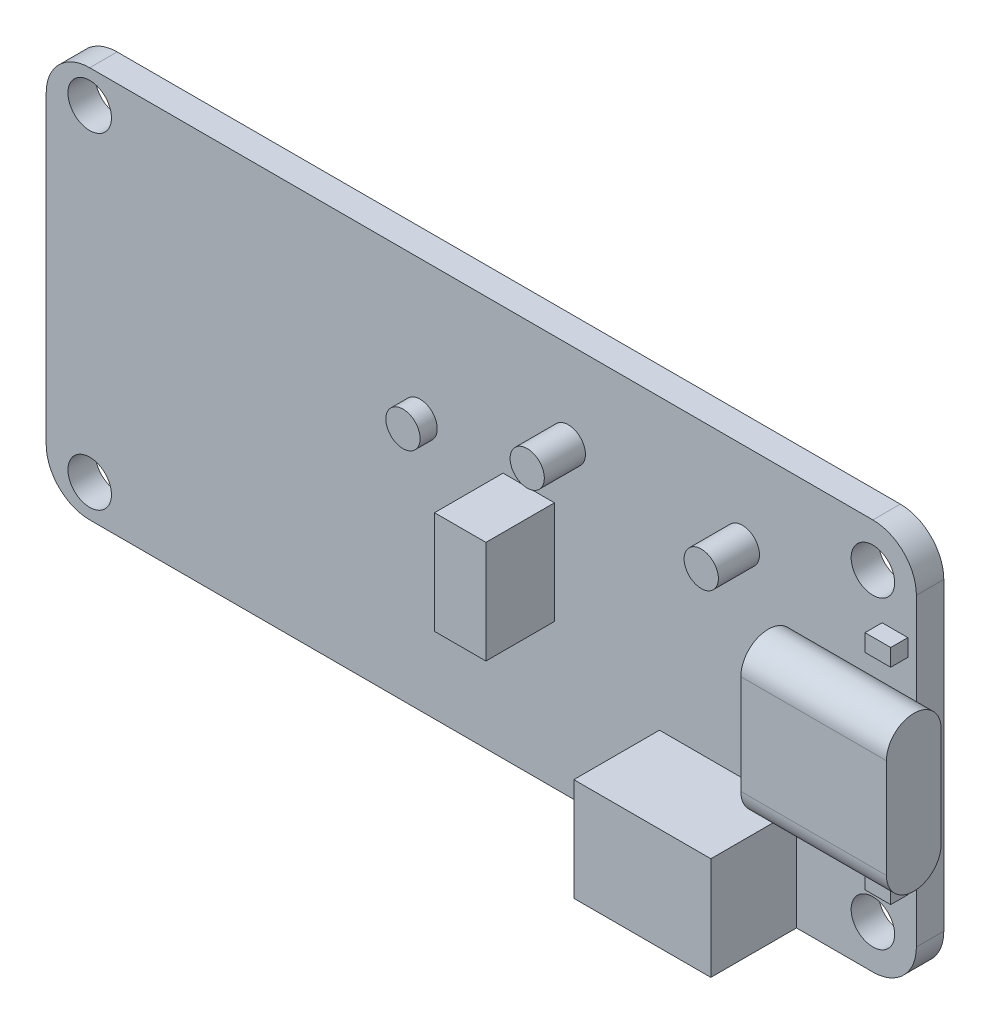
SolidWorks part; units mm, degrees
material "Unlegierter Baustahl"
ref_plane "Ebene vorne" through (0, 0, 0) normal (0, 0, 1) x (1, 0, 0)
ref_plane "Ebene oben" through (0, 0, 0) normal (0, 1, 0) x (1, 0, 0)
ref_plane "Ebene rechts" through (0, 0, 0) normal (1, 0, 0) x (0, 0, -1)
sketch "Skizze1" plane through (0, 0, 0) normal (0, 0, 1) x (1, 0, 0)
  line L1 (-22.86, -11.43) -> (22.86, -11.43)
  line L2 (-25.4, -8.89) -> (-25.4, 8.89)
  line L3 (-22.86, 11.43) -> (22.86, 11.43)
  line L4 (25.4, -8.89) -> (25.4, 8.89)
  line L5 (-25.4, -11.43) -> (25.4, 11.43) construction
  line L6 (-25.4, 11.43) -> (25.4, -11.43) construction
  arc A0 (-25.4, 8.89) -> (-22.86, 11.43) centre (-22.86, 8.89) cw
  arc A1 (-22.86, -11.43) -> (-25.4, -8.89) centre (-22.86, -8.89) cw
  arc A2 (22.86, -11.43) -> (25.4, -8.89) centre (22.86, -8.89) ccw
  arc A3 (22.86, 11.43) -> (25.4, 8.89) centre (22.86, 8.89) cw
  point P0 (0, 0)
  dimension "D3" = 2.54
  dimension "D1" = 50.8
  dimension "D2" = 22.86
extrude "board" add sketch "Skizze1" along normal blind 1.6
hole_wizard "Durchgangsloch für M21" positions "Skizze2" profile "Skizze3" hole size "M2" standard "DIN" end condition through all
sketch "Skizze2" plane through (0, 0, 1.6) normal (0, 0, 1) x (1, 0, 0)
  line L4 (22.86, -9.525) -> (-22.86, -9.525) construction
  line L5 (22.86, -9.525) -> (22.86, 9.525) construction
  line L6 (22.86, 9.525) -> (-22.86, 9.525) construction
  line L7 (-22.86, -9.525) -> (-22.86, 9.525) construction
  line L8 (22.86, -9.525) -> (-22.86, 9.525) construction
  line L9 (22.86, 9.525) -> (-22.86, -9.525) construction
  point P12 (-22.86, 9.525)
  point P14 (-22.86, -9.525)
  point P123 (22.86, 8.89)
  point P125 (22.86, -8.89)
  dimension "D1" = 19.05
  dimension "D2" = 45.72
  dimension "D3" = 8.89
  dimension "D4" = 8.89
sketch "Skizze3" plane through (-22.86, 9.525, 1.6) normal (1, 0, 0) x (0, -1, 0)
  line L0 (0, 0) -> (0, 1.6)
  line L1 (0, 1.6) -> (1.27, 1.6)
  line L2 (1.27, 1.6) -> (1.27, 0)
  line L5 (1.27, 0) -> (0, 0)
  line L11 (0, -6.35) -> (0, 107.95) construction
  dimension "Bohrerdurchmesser" = 2.54
  dimension "Bohrungstiefe" = 1.6
sketch "Skizze4" plane through (25.4, 0, 0) normal (1, 0, 0) x (0, 0, -1)
  line L0 (-3.25, -2.9) -> (-3.25, 2.9) construction
  line L1 (-4.85, -2.9) -> (-4.85, 2.9)
  line L2 (-1.65, -2.9) -> (-1.65, 2.9)
  line L3 (-1.6, -8.89) -> (-1.6, 8.89) construction
  arc A0 (-4.85, -2.9) -> (-1.65, -2.9) centre (-3.25, -2.9) ccw
  arc A1 (-1.65, 2.9) -> (-4.85, 2.9) centre (-3.25, 2.9) ccw
  point P2 (-3.25, 0)
  point P7 (-3.25, 4.5)
  point P8 (-3.25, -4.5)
  dimension "D1" = 9
  dimension "D2" = 0.05
  dimension "D3" = 3.2
extrude "usbc" add sketch "Skizze4" along normal blind 1.5 and the other way blind 7 separate body
sketch "Skizze5" plane through (0, -11.43, 0) normal (0, -1, 0) x (1, 0, 0)
  line L0 (-22.86, 1.6) -> (22.86, 1.6) construction
  line L1 (10.4, 6.6) -> (18.4, 6.6)
  line L2 (10.4, 6.6) -> (10.4, 1.6)
  line L3 (10.4, 1.6) -> (18.4, 1.6)
  line L4 (18.4, 6.6) -> (18.4, 1.6)
  line L5 (10.4, 6.6) -> (18.4, 1.6) construction
  line L6 (10.4, 1.6) -> (18.4, 6.6) construction
  line L8 (25.4, 1.6) -> (25.4, 0) construction
  point P0 (14.4, 4.1)
  dimension "D1" = 5
  dimension "D2" = 15
  dimension "D3" = 8
extrude "battery" add sketch "Skizze5" against normal blind 6
sketch "Skizze6" plane through (0, 0, 1.6) normal (0, 0, 1) x (1, 0, 0)
  line L0 (25.4, -8.89) -> (25.4, 8.89) construction
  line L1 (22.86, 11.43) -> (-22.86, 11.43) construction
  line L2 (18.4, -11.43) -> (22.86, -11.43) construction
  circle A0 centre (15.24, 6.35) radius 1
  circle A1 centre (5.08, 6.35) radius 1
  dimension "D6" = 2
  dimension "D1" = 10.16
  dimension "D2" = 20.32
  dimension "D3" = 17.78
  dimension "D5" = 5.08
extrude "buttons" add sketch "Skizze6" along normal blind 2.4
sketch "Skizze7" plane through (0, 0, 1.6) normal (0, 0, 1) x (1, 0, 0)
  line L0 (25.4, -8.89) -> (25.4, 8.89) construction
  line L1 (4.27, -3) -> (1.27, -3)
  line L2 (4.27, -3) -> (4.27, 3)
  line L3 (4.27, 3) -> (1.27, 3)
  line L4 (1.27, -3) -> (1.27, 3)
  line L5 (4.27, -3) -> (1.27, 3) construction
  line L6 (4.27, 3) -> (1.27, -3) construction
  point P0 (2.77, 0)
  dimension "D1" = 24.13
  dimension "D2" = 6
  dimension "D3" = 3
extrude "qwiic" add sketch "Skizze7" along normal blind 4
sketch "Skizze8" plane through (0, 0, 1.6) normal (0, 0, 1) x (1, 0, 0)
  line L1 (-4.572, 2.318) -> (-2.572, 2.318) construction
  line L2 (-4.572, 2.318) -> (-4.572, 4.318) construction
  line L3 (-4.572, 4.318) -> (-2.572, 4.318) construction
  line L4 (-2.572, 2.318) -> (-2.572, 4.318) construction
  line L5 (-4.572, 2.318) -> (-2.572, 4.318) construction
  line L6 (-4.572, 4.318) -> (-2.572, 2.318) construction
  line L7 (25.4, -8.89) -> (25.4, 8.89) construction
  line L8 (22.86, 11.43) -> (-22.86, 11.43) construction
  circle A0 centre (-3.572, 3.318) radius 1
  point P0 (-3.572, 3.318)
  dimension "D1" = 29.972
  dimension "D2" = 2
  dimension "D3" = 2
  dimension "D4" = 7.112
extrude "neopixel" add sketch "Skizze8" along normal blind 1
sketch "Skizze9" plane through (0, 0, 1.6) normal (0, 0, 1) x (1, 0, 0)
  line L0 (25.4, -8.89) -> (25.4, 8.89) construction
  line L1 (23.4, 5.5) -> (24.9, 5.5)
  line L2 (23.4, 5.5) -> (23.4, 6.5)
  line L3 (23.4, 6.5) -> (24.9, 6.5)
  line L4 (24.9, 5.5) -> (24.9, 6.5)
  line L5 (23.4, 5.5) -> (24.9, 6.5) construction
  line L6 (23.4, 6.5) -> (24.9, 5.5) construction
  line L7 (23.4, -6.5) -> (24.9, -6.5)
  line L8 (23.4, -6.5) -> (23.4, -5.5)
  line L9 (23.4, -5.5) -> (24.9, -5.5)
  line L10 (24.9, -6.5) -> (24.9, -5.5)
  line L11 (23.4, -6.5) -> (24.9, -5.5) construction
  line L12 (23.4, -5.5) -> (24.9, -6.5) construction
  point P0 (24.15, 6)
  point P5 (24.15, -6)
  point P13 (22.5146, -5.5992)
  dimension "D1" = 0.5
  dimension "D2" = 6
  dimension "D3" = 6
  dimension "D4" = 1
  dimension "D5" = 1.5
extrude "leds" add sketch "Skizze9" along normal blind 1
equation "\"D4@Skizze2\"=\"D3@Skizze2\""
